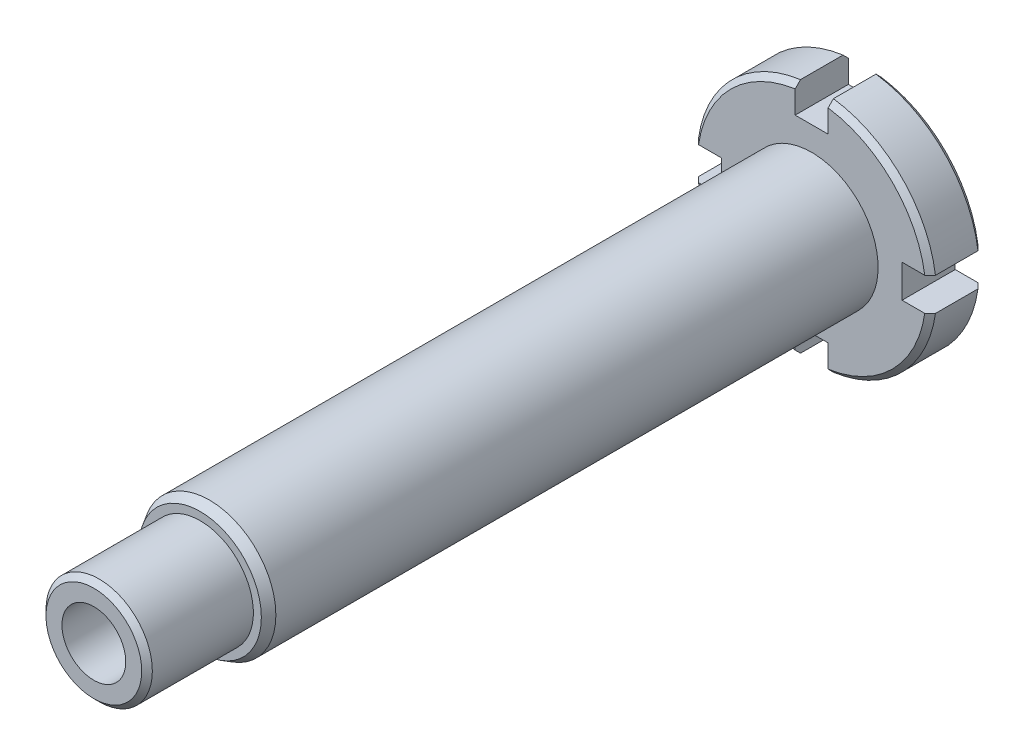
SolidWorks part; units mm, degrees
material "1.7014 (17CrS3)"
ref_plane "Plan de face" through (0, 0, 0) normal (0, 0, 1) x (1, 0, 0)
ref_plane "Plan de dessus" through (0, 0, 0) normal (0, 1, 0) x (1, 0, 0)
ref_plane "Plan de droite" through (0, 0, 0) normal (1, 0, 0) x (0, 0, -1)
sketch "Esquisse1" plane through (0, 0, 0) normal (1, 0, 0) x (0, 0, -1)
  line L0 (0, 0) -> (-113.6905, 0) construction
  line L1 (-145, 0) -> (-145, 10)
  line L2 (-125, 12.5) -> (-10, 12.5)
  line L3 (-10, 12.5) -> (-10, 22.5)
  line L4 (-10, 22.5) -> (0, 22.5)
  line L5 (0, 22.5) -> (0, 0)
  line L6 (0, 0) -> (-145, 0)
  line L7 (-125, 12.5) -> (-125, 10)
  line L8 (-125, 10) -> (-145, 10)
  dimension "D1" = 10
  dimension "D2" = 12.5
  dimension "D3" = 22.5
  dimension "D4" = 115
  dimension "D5" = 20
  dimension "D6" = 10
revolve "Révolution1" add sketch "Esquisse1" angle 360 about L0
cosmetic thread "Représentation de filetage1" parameters "D1"=20, "D2"=17.252
sketch "Esquisse2" plane through (0, 0, 0) normal (0, 0, -1) x (-1, 0, 0)
  line L0 (0, 0) -> (0, 15.963) construction
  line L1 (-3.1, 22.2854) -> (-3.1, 17)
  line L2 (-3.1, 17) -> (3.1, 17)
  line L3 (3.1, 17) -> (3.1, 22.2854)
  circle A0 centre (0, 0) radius 22.5 construction
  arc A3 (3.1, 22.2854) -> (-3.1, 22.2854) centre (0, 0) ccw
  dimension "D2" = 17
  dimension "D1" = 6.2
chamfer "Chanfrein1" distance 1 angle 45 3 edges at (-10, 0, 145) (-22.5, 0, 10) (-22.5, 0, 0)
sketch "Esquisse3" plane through (0, 0, 0) normal (0, 0, -1) x (-1, 0, 0)
  circle A0 centre (0, 0) radius 6
  dimension "D1" = 12
extrude "Enlèv. mat.-Extru.2" cut sketch "Esquisse3" against normal through all
extrude "Enlèv. mat.-Extru.1" cut sketch "Esquisse2" against normal through all
pattern_circular "Répétition circulaire1" count 4 over 360 about axis through (0, 0, 0) along (0, 0, 1) of "Enlèv. mat.-Extru.1"
chamfer "Chanfrein2" distance 1 angle 60 1 edges at (-12.5, 0, 125)
